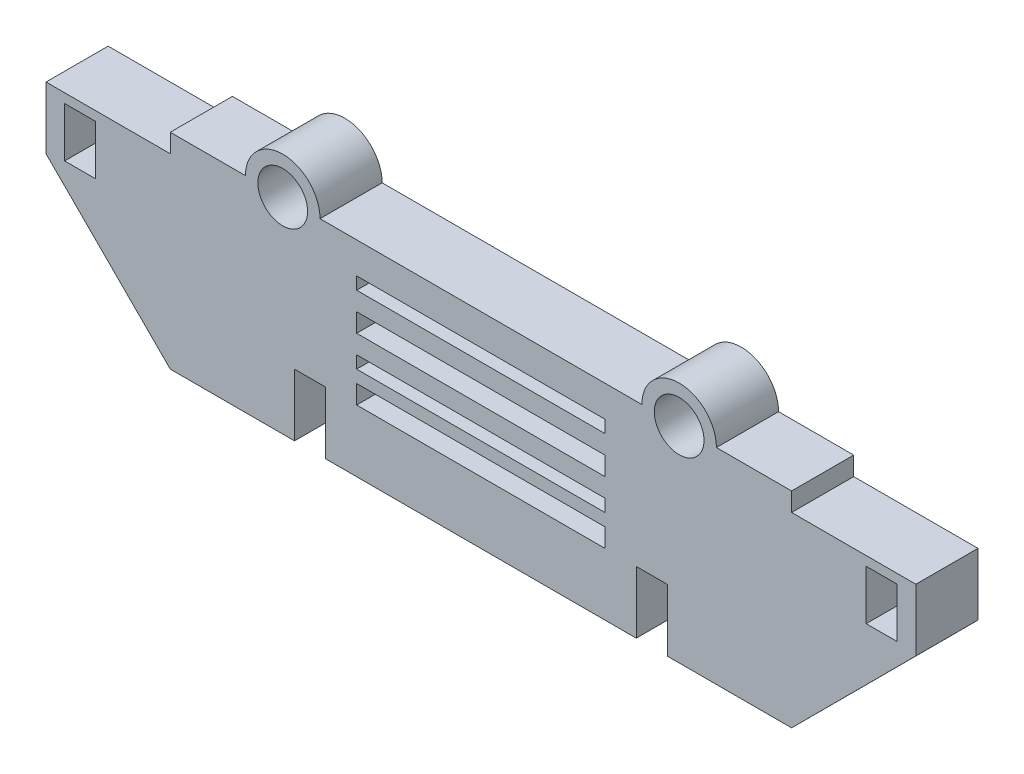
SolidWorks part; units mm, degrees
ref_plane "Alzado" through (0, 0, 0) normal (0, 0, 1) x (1, 0, 0)
ref_plane "Planta" through (0, 0, 0) normal (0, 1, 0) x (1, 0, 0)
ref_plane "Vista lateral" through (0, 0, 0) normal (1, 0, 0) x (0, 0, -1)
sketch "Croquis1" plane through (0, 0, 0) normal (0, 0, 1) x (1, 0, 0)
  line L0 (-25, 0) -> (25, 0)
  line L1 (-25, 0) -> (-25, 10)
  line L2 (-25, 10) -> (-30, 10)
  line L3 (-30, 10) -> (-30, 0)
  line L4 (-30, 0) -> (-50, 0)
  line L5 (-50, 0) -> (-70, 20.0222)
  line L6 (-70, 20.0222) -> (-70, 30.0222)
  line L7 (-70, 30.0222) -> (-50, 30.0222)
  line L8 (-50, 30.0222) -> (-50, 33.0222)
  line L9 (-50, 33.0222) -> (-35.9, 33.0222)
  line L11 (-25.9, 33.0222) -> (25.9, 33.0222)
  line L12 (50, 33.0222) -> (35.9, 33.0222)
  line L13 (50, 30.0222) -> (50, 33.0222)
  line L14 (70, 30.0222) -> (50, 30.0222)
  line L15 (70, 20.0222) -> (70, 30.0222)
  line L16 (50, 0) -> (70, 20.0222)
  line L17 (30, 0) -> (50, 0)
  line L18 (30, 10) -> (30, 0)
  line L19 (25, 10) -> (30, 10)
  line L20 (25, 0) -> (25, 10)
  line L22 (34.5458, 30.0222) -> (30.9, 30.0222) construction
  line L23 (-67, 20.5222) -> (-62, 20.5222)
  line L24 (-20, 10) -> (20, 10)
  line L25 (-20, 10) -> (-20, 13)
  line L26 (-20, 13) -> (20, 13)
  line L27 (20, 10) -> (20, 13)
  line L28 (-20, 15) -> (20, 15)
  line L29 (-20, 15) -> (-20, 17)
  line L30 (-20, 17) -> (20, 17)
  line L31 (20, 15) -> (20, 17)
  line L32 (-20, 20) -> (20, 20)
  line L33 (-20, 20) -> (-20, 23)
  line L34 (-20, 23) -> (20, 23)
  line L35 (20, 20) -> (20, 23)
  line L36 (-20, 26) -> (20, 26)
  line L37 (-20, 26) -> (-20, 28)
  line L38 (-20, 28) -> (20, 28)
  line L39 (20, 26) -> (20, 28)
  line L40 (67, 28.5222) -> (62, 28.5222)
  line L41 (67, 28.5222) -> (67, 20.5222)
  line L42 (67, 20.5222) -> (62, 20.5222)
  line L43 (62, 28.5222) -> (62, 20.5222)
  line L44 (-62, 28.5222) -> (-62, 20.5222)
  line L45 (-67, 28.5222) -> (-62, 28.5222)
  line L46 (-67, 28.5222) -> (-67, 20.5222)
  circle A0 centre (31.9, 33.0222) radius 4
  arc A1 (37.9, 33.0222) -> (25.9, 33.0222) centre (31.9, 33.0222) ccw
  circle A2 centre (-31.9, 33.0222) radius 4
  arc A3 (-37.9, 33.0222) -> (-25.9, 33.0222) centre (-31.9, 33.0222) cw
  point P4 (0, 0)
  dimension "D1" = 50
  dimension "D2" = 10
  dimension "D3" = 20
  dimension "D6" = 20
  dimension "D8" = 28.3
  dimension "D10" = 18.1
  dimension "D11" = 140
  dimension "D12" = 3
  dimension "D14" = 5
  dimension "D27" = 3
extrude "Saliente-Extruir1" add sketch "Croquis1" along normal blind 10
